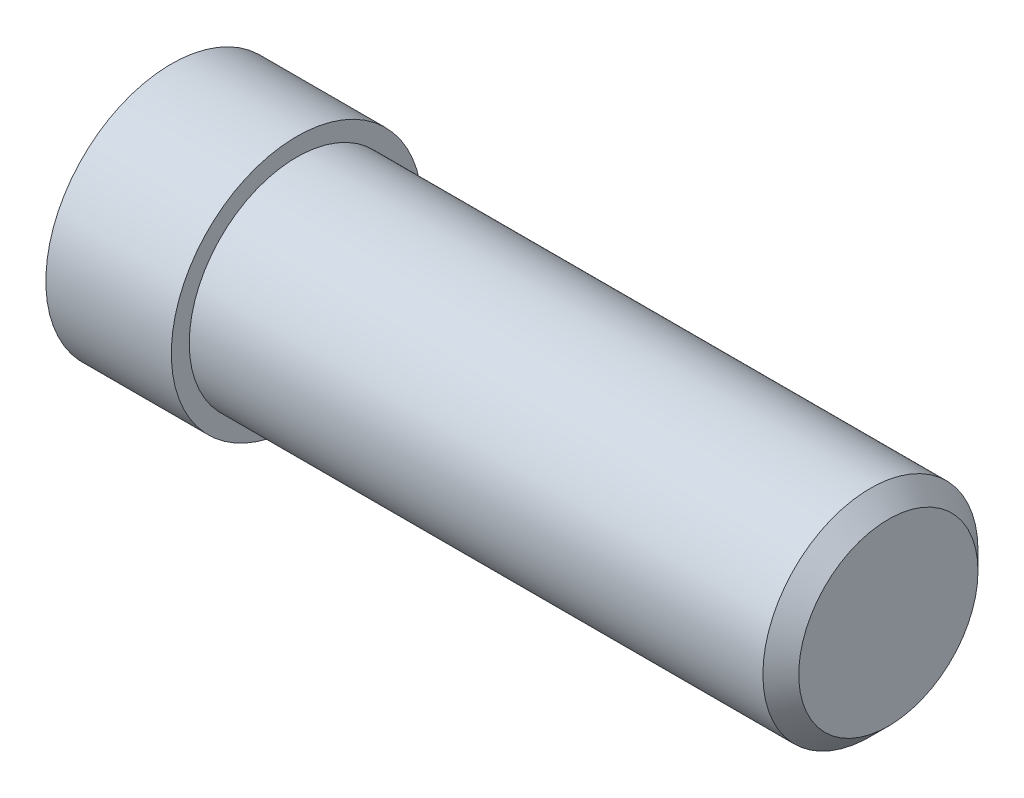
SolidWorks part; units mm, degrees
ref_plane "Ön Düzlem" through (0, 0, 0) normal (0, 0, 1) x (1, 0, 0)
ref_plane "Üst Düzlem" through (0, 0, 0) normal (0, 1, 0) x (1, 0, 0)
ref_plane "Sağ Düzlem" through (0, 0, 0) normal (1, 0, 0) x (0, 0, -1)
sketch "Çizim1" plane through (0, 0, 0) normal (0, 0, 1) x (1, 0, 0)
  line L0 (49.5593, 0) -> (-49.5593, 0) construction
  line L1 (0, 0) -> (0, 7)
  line L2 (0, 7) -> (7, 7)
  line L3 (7, 7) -> (7, 6)
  line L4 (7, 6) -> (40, 6)
  line L5 (40, 6) -> (40, 0)
  line L6 (0, 0) -> (40, 0)
  point P4 (0, 0)
  dimension "D1" = 7
  dimension "D2" = 7
  dimension "D3" = 33
  dimension "D4" = 6
revolve "Döndür1" add sketch "Çizim1" angle 360 about L0
chamfer "Pah1" distance 1 angle 45 1 edges at (40, 0, -6)
